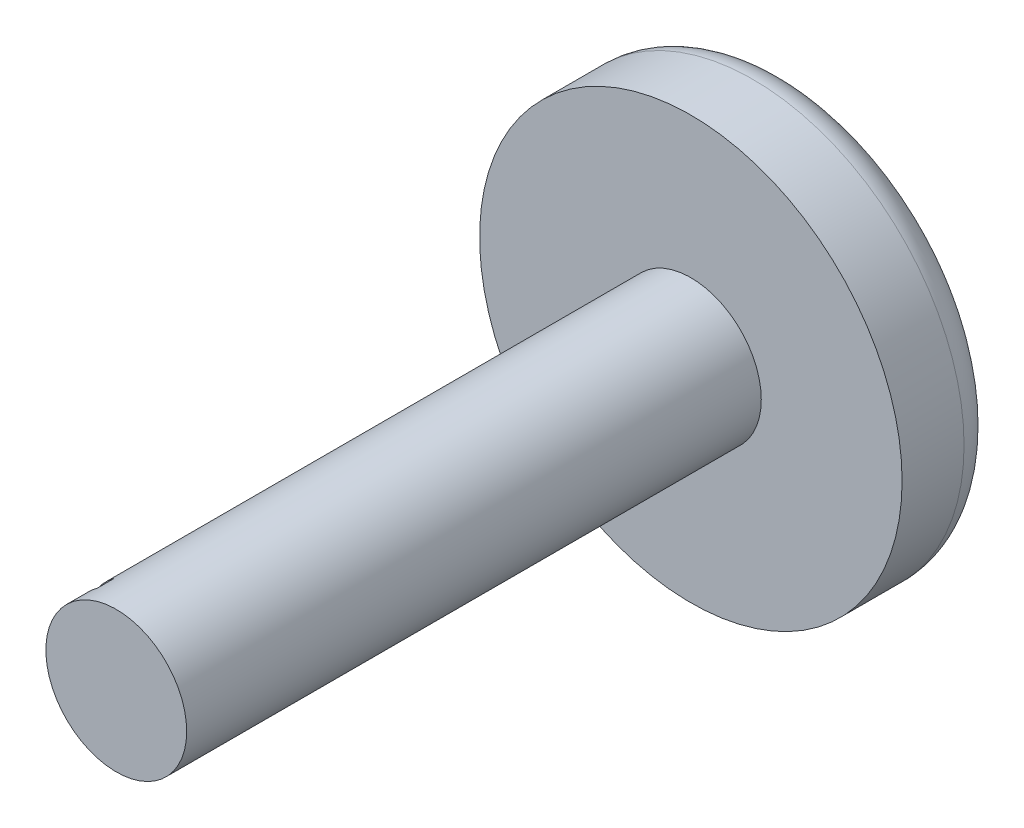
SolidWorks part; units mm, degrees
material "Stainless Steel (ferritic)"
ref_plane "Front Plane" through (0, 0, 0) normal (0, 0, 1) x (1, 0, 0)
ref_plane "Top Plane" through (0, 0, 0) normal (0, 1, 0) x (1, 0, 0)
ref_plane "Right Plane" through (0, 0, 0) normal (1, 0, 0) x (0, 0, -1)
sketch "Sketch1" plane through (0, 0, 0) normal (0, 0, 1) x (1, 0, 0)
  circle A0 centre (0, 0) radius 3.75
  dimension "D1" = 7.5
extrude "Boss-Extrude1" add sketch "Sketch1" along normal blind 11.9
sketch "Sketch2" plane through (0, 0, 11.9) normal (0, 0, 1) x (1, 0, 0)
  circle A0 centre (0, 0) radius 1.25
  circle A1 centre (0, 0) radius 3.75 construction
  circle A2 centre (0, 0) radius 3.75
  dimension "D1" = 2.5
extrude "Cut-Extrude1" cut sketch "Sketch2" against normal blind 10.2
fillet "Fillet1" radius 0.6 1 edges at (3.75, 0, 0)
ref_plane "Plane1" through (0, 0, 11.5) normal (0, 0, 1) x (1, 0, 0)
sketch "Sketch3" plane through (0, 0, 11.5) normal (0, 0, 1) x (1, 0, 0)
  line L0 (0, 0.4664) -> (-0.7321, 1.0132)
  line L3 (0, -0.4664) -> (-0.7321, -1.0132)
  line L4 (0, -0.4664) -> (0, 0.4664)
  circle A1 centre (0, 0) radius 1.25 construction
  arc A2 (-0.7321, 1.0132) -> (-0.7321, -1.0132) centre (0, 0) ccw
  point P8 (0, 0)
extrude "Cut-Extrude2" cut sketch "Sketch3" against normal blind 0.3
